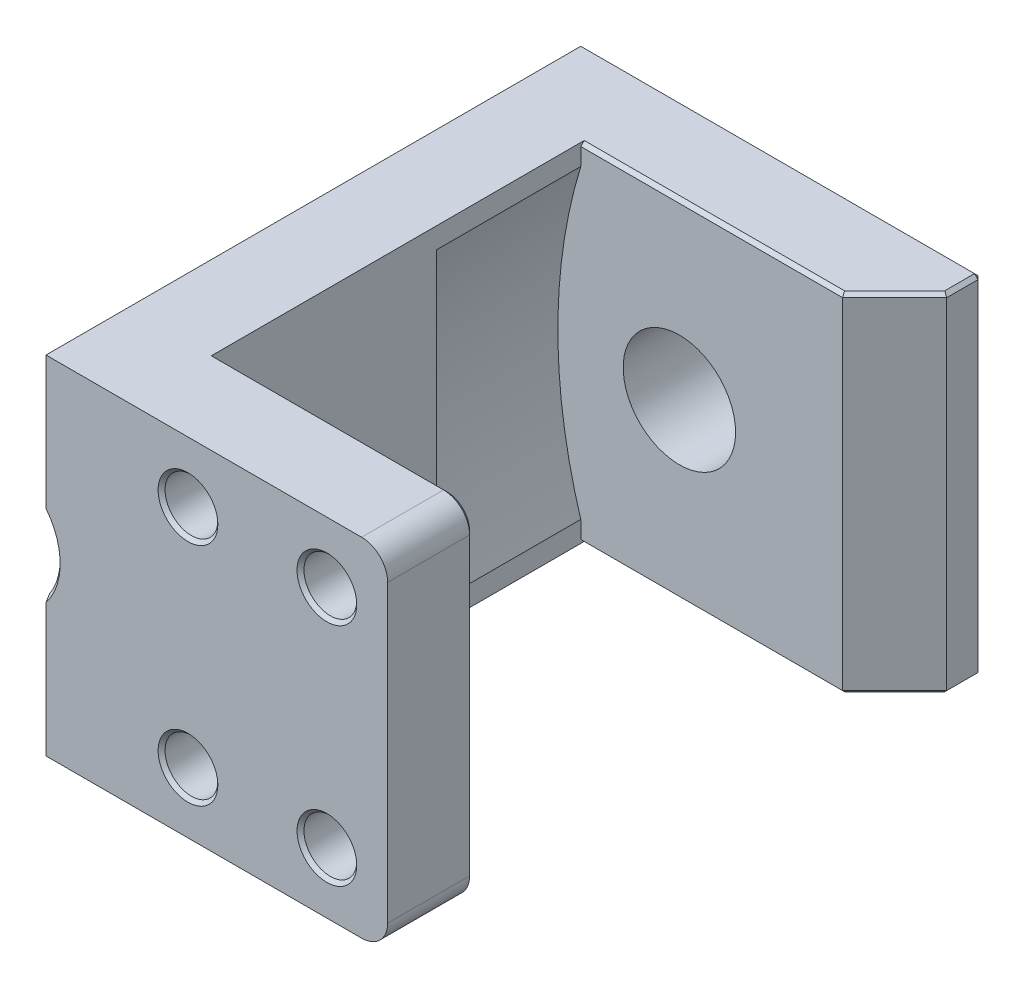
SolidWorks part; units mm, degrees
other "标注1"
sketch "草图9" plane through (-10.48, 10, -1.55) normal (-0.4516, 0.1897, -0.8718) x (-0.888, 0, 0.4599)
material "7075-T6 (SN)"
ref_plane "前视基准面" through (0, 0, 0) normal (0, 0, 1) x (1, 0, 0)
ref_plane "上视基准面" through (0, 0, 0) normal (0, 1, 0) x (1, 0, 0)
ref_plane "右视基准面" through (0, 0, 0) normal (1, 0, 0) x (0, 0, -1)
sketch "草图1" plane through (0, 0, 0) normal (0, 0, 1) x (1, 0, 0)
  line L1 (13.5775, 0) -> (13.5775, 10)
  line L2 (13.5775, 0) -> (13.5775, -10)
  line L4 (-10.48, 0) -> (-10.48, 10)
  line L5 (-10.48, 10) -> (13.5775, 10)
  line L6 (13.5775, -10) -> (-10.48, -10)
  line L7 (-10.48, -10) -> (-10.48, 0)
  circle A0 centre (0, 0) radius 3.2375
extrude "凸台-拉伸1" add sketch "草图1" along normal blind 5
sketch "草图2" plane through (0, 0, 0) normal (0, 0, 1) x (1, 0, 0)
  circle A0 centre (0, 5.6) radius 1.015
  circle A1 centre (0, -5.6) radius 1.015
extrude "切除-拉伸1" cut sketch "草图2" along normal blind 2.85
chamfer "倒角1" distance 0.2 angle 45 2 edges at (1.015, -5.6, 0) (1.015, 5.6, 0)
sketch "草图5" plane through (0, 0, 0) normal (0, 0, 1) x (1, 0, 0)
  line L0 (-9, 7.275) -> (-10.48, 7.275)
  line L2 (-9, 0) -> (-9, 7.275)
  line L3 (-9, 0) -> (-9, -7.275)
  line L4 (-10.48, 10) -> (-10.48, -10) construction
  line L5 (-10.48, 7.275) -> (-10.48, -7.275)
  line L6 (-10.48, -7.275) -> (-9, -7.275)
extrude "凸台-拉伸2" add sketch "草图5" against normal blind 1.55 from surface at 0 starting at face at (-1.215, -5.6, 0)
chamfer "倒角2" distance 0.2 angle 45 4 edges at (-9.74, -7.275, -1.55) (-9, 0, -1.55) (-10.48, 0, -1.55) (-9.74, 7.275, -1.55)
fillet "圆角1" radius 0.15 4 edges at (-10.48, -7.275, -0.675) (-9, -7.275, -0.675) (-9, 7.275, -0.675) (-10.48, 7.275, -0.675)
sketch "草图6" plane through (0, 0, 0) normal (0, 0, 1) x (1, 0, 0)
  line L1 (13.5775, 10) -> (-10.48, 10) construction
  line L3 (-10.48, -10) -> (13.5775, -10) construction
  line L6 (-10.48, 10) -> (-5.68, 10)
  line L7 (-10.48, 10) -> (-10.48, -10)
  line L8 (-10.48, -10) -> (-5.68, -10)
  line L9 (-5.68, -10) -> (-5.68, 10)
extrude "凸台-拉伸3" add sketch "草图6" along normal blind 31
sketch "草图7" plane through (0, 0, 0) normal (0, 0, 1) x (1, 0, 0)
  line L1 (13.5775, 10) -> (-5.68, 10) construction
  line L2 (-6.3225, 10) -> (-6.3225, -10)
  line L3 (-5.68, -10) -> (13.5775, -10) construction
  line L6 (-6.3225, 10) -> (13.5775, 10)
  line L7 (13.5775, 10) -> (13.5775, -10)
  line L8 (13.5775, -10) -> (-6.3225, -10)
extrude "凸台-拉伸4" add sketch "草图7" against normal blind 4.92 from surface at 31 starting at face at (-8.08, 0, 31)
sketch "草图8" plane through (0, 0, 0) normal (0, 0, 1) x (1, 0, 0)
  circle A4 centre (-2.3025, 6.5) radius 1.52
  circle A5 centre (5.6975, 6.5) radius 1.52
  circle A6 centre (5.6975, -6.5) radius 1.52
  circle A7 centre (-2.3025, -6.5) radius 1.52
extrude "切除-拉伸2" cut sketch "草图8" against normal up to surface (4.92 mm away) from surface
chamfer "倒角3" distance 0.2 angle 45 4 edges at (-0.7825, -6.5, 31) (7.2175, -6.5, 31) (7.2175, 6.5, 31) (-0.7825, 6.5, 31)
sketch "草图10" plane through (0, 0, 0) normal (0, 0, 1) x (1, 0, 0)
  line L0 (9.199, 6.5) -> (9.199, -10)
  line L1 (-10.48, -10) -> (13.5775, -10) construction
  line L2 (9.199, 6.5) -> (9.199, 10)
  line L3 (13.5775, 10) -> (-10.48, 10) construction
  line L4 (9.199, 10) -> (13.5775, 10)
  line L5 (13.5775, 10) -> (13.5775, -10)
  line L6 (13.5775, -10) -> (9.199, -10)
extrude "切除-拉伸3" cut sketch "草图10" against normal up to surface (31 mm away) from surface at 31 up to face at (-5.9771, 0, 0) starting at face at (-0.5825, -6.5, 31)
fillet "圆角2" radius 1.5 2 edges at (9.199, -10, 28.54) (9.199, 10, 28.54)
sketch "草图11" plane through (0, 0, 0) normal (0, 0, 1) x (1, 0, 0)
  line L0 (-10.48, 2.0075) -> (-10.48, -2.0075)
  line L1 (-10.48, 10) -> (-10.48, -10) construction
  arc A0 (-10.48, -2.0075) -> (-10.48, 2.0075) centre (-13.4367, 0) ccw
extrude "切除-拉伸4" cut sketch "草图11" against normal blind 1.5 from surface at 31 starting at face at (-0.5825, -6.5, 31)
chamfer "倒角4" distance 0.2 angle 45 7 edges at (-10.48, 0, 29.5) (-9.8629, 0, 31) (1.0095, -10, 26.08) (8.7596, -9.5607, 26.08) (9.199, 0, 26.08) (8.7596, 9.5607, 26.08) (1.0095, 10, 26.08)
sketch "草图13" plane through (0, 0, 0) normal (0, 0, 1) x (1, 0, 0)
  line L0 (9.199, 10) -> (9.199, -10)
  line L1 (9.199, -10) -> (12.399, -10)
  line L2 (9.199, 10) -> (12.399, 10)
  line L3 (12.399, 10) -> (12.399, -10)
extrude "凸台-拉伸5" add sketch "草图13" along normal up to surface (5 mm away) from surface at 0 up to face at (3.2375, 0, 5) starting at face at (-1.215, -5.6, 0)
chamfer "倒角5" distance 3 angle 45 1 edges at (12.399, 0, 5)
sketch "草图14" plane through (0, 0, 0) normal (0, 0, 1) x (1, 0, 0)
  line L1 (7.699, 10) -> (-10.48, 10) construction
  line L2 (-10.48, -10) -> (7.699, -10) construction
  line L3 (-5.2843, 10) -> (-5.2843, -10)
  arc A4 (-5.2843, 10) -> (-5.2843, -10) centre (23, 0) ccw
extrude "切除-拉伸5" cut sketch "草图14" along normal blind 7 from surface at 5 starting at face at (3.2375, 0, 5)
chamfer "倒角7" distance 1.3 angle 45 1 edges at (-5.68, 0, 12)
chamfer "倒角8" distance 0.2 angle 45 9 edges at (0.9595, -10, 0) (0.9595, 10, 0) (1.8595, 10, 5) (10.899, 10, 3.5) (12.399, 10, 1) (12.399, 0, 0) (12.399, -10, 1) (10.899, -10, 3.5) (1.8595, -10, 5)
